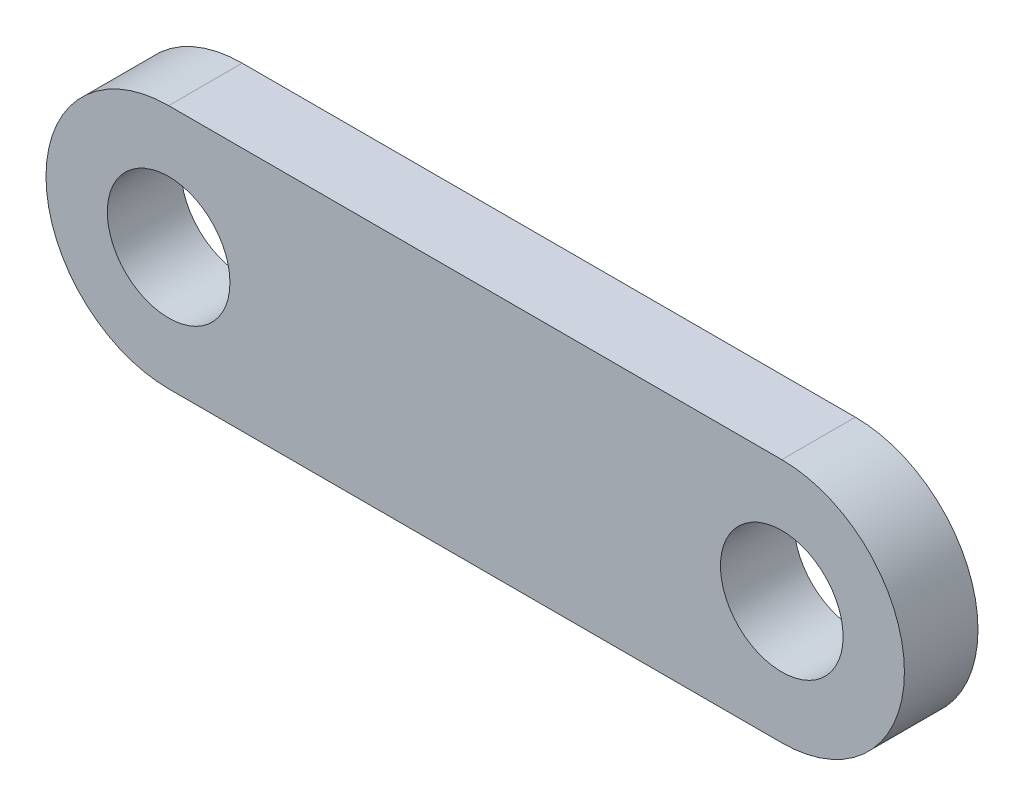
SolidWorks part; units mm, degrees
ref_plane "Front Plane" through (0, 0, 0) normal (0, 0, 1) x (1, 0, 0)
ref_plane "Top Plane" through (0, 0, 0) normal (0, 1, 0) x (1, 0, 0)
ref_plane "Right Plane" through (0, 0, 0) normal (1, 0, 0) x (0, 0, -1)
sketch "Sketch1" plane through (0, 0, 0) normal (0, 0, 1) x (1, 0, 0)
  line L0 (-12.5, 0) -> (12.5, 0) construction
  line L1 (-12.5, 5) -> (12.5, 5)
  line L2 (-12.5, -5) -> (12.5, -5)
  arc A0 (-12.5, 5) -> (-12.5, -5) centre (-12.5, 0) ccw
  arc A1 (12.5, -5) -> (12.5, 5) centre (12.5, 0) ccw
  circle A2 centre (12.5, 0) radius 2.5
  circle A3 centre (-12.5, 0) radius 2.5
  point P2 (0, 0)
  dimension "D1" = 5
  dimension "D3" = 5
  dimension "D2" = 25
extrude "Boss-Extrude1" add sketch "Sketch1" along normal blind 3
